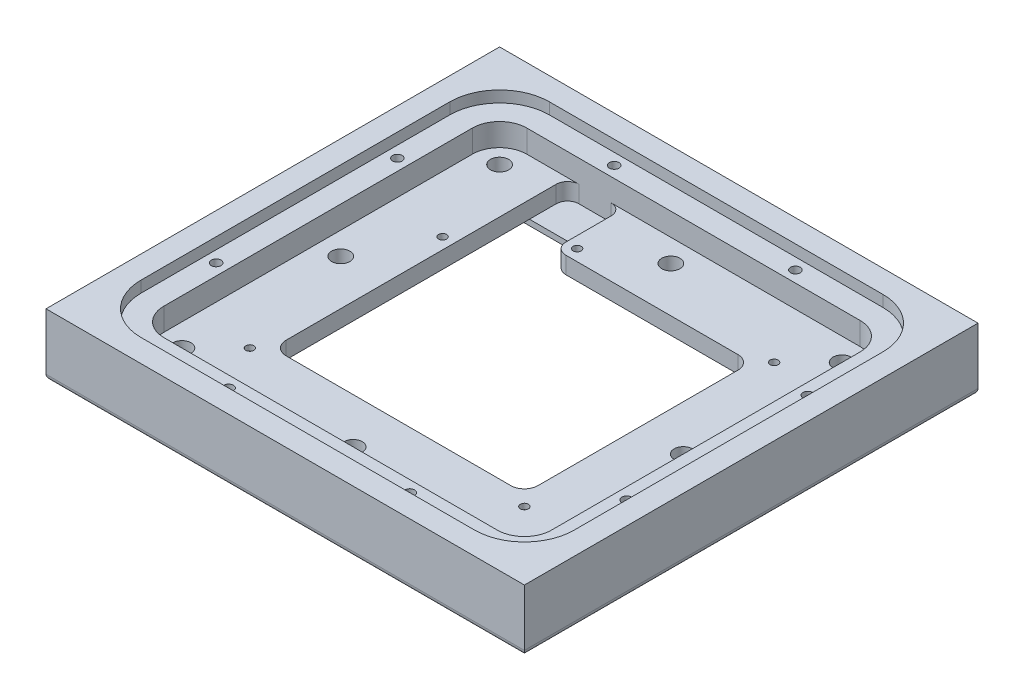
SolidWorks part; units mm, degrees
material "PE High Density"
ref_plane "Front Plane" through (0, 0, 0) normal (0, 0, 1) x (1, 0, 0)
ref_plane "Top Plane" through (0, 0, 0) normal (0, 1, 0) x (1, 0, 0)
ref_plane "Right Plane" through (0, 0, 0) normal (1, 0, 0) x (0, 0, -1)
sketch "Sketch2" plane through (0, 0, 0) normal (0, 1, 0) x (1, 0, 0)
  line L0 (-41.656, 22.1996) -> (-19.9136, 22.1996)
  line L1 (41.656, -38.1762) -> (-41.656, -38.1762)
  line L2 (41.656, -38.1762) -> (41.656, 38.1762)
  line L3 (41.656, 38.1762) -> (-41.656, 38.1762)
  line L4 (-41.656, -38.1762) -> (-41.656, 38.1762)
  line L5 (41.656, -38.1762) -> (-41.656, 38.1762) construction
  line L6 (41.656, 38.1762) -> (-41.656, -38.1762) construction
  line L7 (-19.9136, 22.1996) -> (-19.9136, 38.1762)
  line L8 (67.056, -63.5762) -> (-67.056, -63.5762)
  line L9 (-67.056, -63.5762) -> (-67.056, 63.5762)
  line L10 (67.056, 63.5762) -> (-67.056, 63.5762)
  line L11 (67.056, -63.5762) -> (67.056, 63.5762)
  point P0 (0, 0)
  point P13 (-38.481, -35.0012)
  point P14 (38.481, -35.0012)
  point P15 (38.481, 35.0012)
  point P16 (-16.7386, 35.0012)
  point P17 (-38.481, 19.0246)
  dimension "D1" = 83.312
  dimension "D2" = 76.3524
  dimension "D3" = 21.7424
  dimension "D4" = 15.9766
  dimension "D6" = 3.175
  dimension "D7" = 3.175
  dimension "D8" = 57.2008
  dimension "D9" = 80.137
  dimension "D10" = 24.9174
  dimension "D11" = 73.1774
  dimension "D5" = 25.4
extrude "Boss-Extrude1" add sketch "Sketch2" along normal blind 15.875 contours L8 L11 L10 L9 L1 L4 L3 L2 | L0 L7 L3 L4
sketch "Sketch4" plane through (0, 0, 0) normal (0, 1, 0) x (1, 0, 0)
  line L0 (41.656, -38.1762) -> (41.656, 38.1762) construction
  line L1 (41.656, 38.1762) -> (-19.9136, 38.1762) construction
  line L2 (41.656, -38.1762) -> (-41.656, -38.1762) construction
  line L3 (-41.656, -38.1762) -> (-41.656, 22.1996) construction
  line L4 (-41.656, 22.1996) -> (-19.9136, 22.1996) construction
  line L5 (41.656, -38.1762) -> (41.656, 38.1762)
  line L6 (41.656, 38.1762) -> (-19.9136, 38.1762)
  line L7 (41.656, -38.1762) -> (-41.656, -38.1762)
  line L8 (-41.656, -38.1762) -> (-41.656, 22.1996)
  line L9 (-41.656, 22.1996) -> (-19.9136, 22.1996)
  line L10 (-19.9136, 22.1996) -> (-19.9136, 38.1762) construction
  line L11 (-19.9136, 22.1996) -> (-19.9136, 38.1762)
  line L12 (35.306, 31.8262) -> (-13.5636, 31.8262)
  line L13 (-13.5636, 15.8496) -> (-13.5636, 31.8262)
  line L14 (-35.306, 15.8496) -> (-13.5636, 15.8496)
  line L15 (-35.306, -31.8262) -> (-35.306, 15.8496)
  line L16 (35.306, -31.8262) -> (-35.306, -31.8262)
  line L17 (35.306, -31.8262) -> (35.306, 31.8262)
  dimension "D1" = 6.35
extrude "Boss-Extrude2" add sketch "Sketch4" along normal blind 9.525
sketch "Sketch5" plane through (0, 0, 0) normal (0, -1, 0) x (1, 0, 0)
  line L5 (46.736, -50.8762) -> (-46.736, -50.8762)
  line L6 (54.356, -43.2562) -> (54.356, 43.2562)
  line L7 (46.736, 50.8762) -> (-46.736, 50.8762)
  line L8 (-54.356, -43.2562) -> (-54.356, 43.2562)
  line L9 (54.356, -50.8762) -> (-54.356, 50.8762) construction
  line L10 (54.356, 50.8762) -> (-54.356, -50.8762) construction
  arc A0 (46.736, -50.8762) -> (54.356, -43.2562) centre (46.736, -43.2562) ccw
  arc A1 (-46.736, -50.8762) -> (-54.356, -43.2562) centre (-46.736, -43.2562) cw
  arc A2 (54.356, 43.2562) -> (46.736, 50.8762) centre (46.736, 43.2562) ccw
  arc A3 (-46.736, 50.8762) -> (-54.356, 43.2562) centre (-46.736, 43.2562) ccw
  point P0 (0, 0)
  dimension "D3" = 7.62
  dimension "D1" = 108.712
  dimension "D2" = 101.7524
extrude "Cut-Extrude2" cut sketch "Sketch5" against normal blind 3.175
hole_wizard "M2.5x0.45 Tapped Hole1" positions "Sketch6" profile "Sketch7" tap size "M2.5x0.45" standard "ANSI Metric"
sketch "Sketch6" plane through (0, 3.175, 0) normal (0, -1, 0) x (-1, 0, 0)
  point P0 (38.481, -35.0012)
  point P3 (-38.481, -35.0012)
  point P6 (38.481, 19.0246)
  point P9 (16.7386, 35.0012)
  point P12 (-38.481, 35.0012)
sketch "Sketch7" plane through (-38.481, 3.175, 35.0012) normal (1, 0, 0) x (0, 0, -1)
  line L0 (0, 0) -> (0, 6.9659)
  line L1 (0, 6.9659) -> (1.025, 6.35)
  line L2 (1.025, 6.35) -> (1.025, 0)
  line L5 (1.025, 0) -> (0, 0)
  line L10 (0, 6.9659) -> (-1.025, 6.35) construction
  line L11 (0, -6.35) -> (0, 107.95) construction
  dimension "Tap Drill Dia." = 2.05
  dimension "Tap Drill Depth" = 6.35
  dimension "Drill Angle" = 118
cosmetic thread "Hole Thread1" parameters "D1"=5.08, "D2"=2.5
cosmetic thread "Hole Thread2" parameters "D1"=5.08, "D2"=2.5
cosmetic thread "Hole Thread3" parameters "D1"=5.08, "D2"=2.5
cosmetic thread "Hole Thread4" parameters "D1"=5.08, "D2"=2.5
cosmetic thread "Hole Thread5" parameters "D1"=5.08, "D2"=2.5
hole_wizard "#10 Clearance Hole1" positions "Sketch8" profile "Sketch9" hole size "#10" standard "ANSI Inch" end condition through all
sketch "Sketch8" plane through (0, 3.175, 0) normal (0, -1, 0) x (-1, 0, 0)
  line L0 (54.356, -43.2562) -> (54.356, 43.2562) construction
  line L1 (-46.736, -50.8762) -> (46.736, -50.8762) construction
  line L2 (46.736, 50.8762) -> (-46.736, 50.8762) construction
  line L3 (-54.356, 43.2562) -> (-54.356, -43.2562) construction
  point P0 (48.006, -44.5262)
  point P2 (0, -44.5262)
  point P4 (-48.006, -44.5262)
  point P6 (-48.006, 0)
  point P8 (-48.006, 44.5262)
  point P10 (0, 44.5262)
  point P12 (48.006, 44.5262)
  point P14 (48.006, 0)
  dimension "D1" = 6.35
  dimension "D2" = 6.35
  dimension "D3" = 6.35
  dimension "D4" = 6.35
sketch "Sketch9" plane through (-48.006, 3.175, 44.5262) normal (1, 0, 0) x (0, 0, -1)
  line L0 (0, 0) -> (0, 12.7)
  line L1 (0, 12.7) -> (2.5527, 12.7)
  line L2 (2.5527, 12.7) -> (2.5527, 0)
  line L5 (2.5527, 0) -> (0, 0)
  line L11 (0, -6.35) -> (0, 107.95) construction
  dimension "Thru Hole Dia." = 5.1054
  dimension "Thru Hole Depth" = 12.7
sketch "Sketch10" plane through (0, 15.875, 0) normal (0, 1, 0) x (1, 0, 0)
  line L4 (54.356, -43.2562) -> (54.356, 43.2562)
  line L5 (-46.736, -50.8762) -> (46.736, -50.8762)
  line L6 (-54.356, 43.2562) -> (-54.356, -43.2562)
  line L7 (46.736, 50.8762) -> (-46.736, 50.8762)
  line L8 (54.356, -43.2562) -> (54.356, 43.2562)
  line L9 (-46.736, -50.8762) -> (46.736, -50.8762)
  line L10 (-54.356, 43.2562) -> (-54.356, -43.2562)
  line L11 (46.736, 50.8762) -> (-46.736, 50.8762)
  arc A4 (54.356, 43.2562) -> (46.736, 50.8762) centre (46.736, 43.2562) ccw
  arc A5 (46.736, -50.8762) -> (54.356, -43.2562) centre (46.736, -43.2562) ccw
  arc A6 (-54.356, -43.2562) -> (-46.736, -50.8762) centre (-46.736, -43.2562) ccw
  arc A7 (-46.736, 50.8762) -> (-54.356, 43.2562) centre (-46.736, 43.2562) ccw
  arc A8 (54.356, 43.2562) -> (46.736, 50.8762) centre (46.736, 43.2562) ccw
  arc A9 (46.736, -50.8762) -> (54.356, -43.2562) centre (46.736, -43.2562) ccw
  arc A10 (-54.356, -43.2562) -> (-46.736, -50.8762) centre (-46.736, -43.2562) ccw
  arc A11 (-46.736, 50.8762) -> (-54.356, 43.2562) centre (-46.736, 43.2562) ccw
  dimension "D1" = 0
extrude "Cut-Extrude3" cut sketch "Sketch10" against normal up to surface (6.35 mm away) up to face at (-38.481, 9.525, 33.9762)
sketch "Sketch11" plane through (0, 3.175, 0) normal (0, -1, 0) x (1, 0, 0)
  line L8 (43.688, 40.2082) -> (-43.688, 40.2082)
  line L9 (-43.688, 40.2082) -> (-43.688, -40.2082)
  line L10 (-43.688, -40.2082) -> (43.688, -40.2082)
  line L11 (43.688, -40.2082) -> (43.688, 40.2082)
  line L12 (40.513, 40.2082) -> (-40.513, 40.2082)
  line L13 (-43.688, 37.0332) -> (-43.688, -37.0332)
  line L14 (-40.513, -40.2082) -> (40.513, -40.2082)
  line L15 (43.688, -37.0332) -> (43.688, 37.0332)
  arc A0 (40.513, -40.2082) -> (43.688, -37.0332) centre (40.513, -37.0332) ccw
  arc A1 (-43.688, -37.0332) -> (-40.513, -40.2082) centre (-40.513, -37.0332) ccw
  arc A2 (40.513, 40.2082) -> (43.688, 37.0332) centre (40.513, 37.0332) cw
  arc A3 (-40.513, 40.2082) -> (-43.688, 37.0332) centre (-40.513, 37.0332) ccw
  point P16 (-40.0685, 39.7637)
  point P17 (-40.0685, 39.7637)
  dimension "D2" = 3.175
  dimension "D1" = 2.032
extrude "Cut-Extrude4" cut sketch "Sketch11" against normal blind 1.6
sketch "Sketch12" plane through (0, 4.775, 0) normal (0, -1, 0) x (1, 0, 0)
  line L0 (-35.306, 31.8262) -> (-35.306, -15.8496) construction
  line L1 (35.306, 31.8262) -> (-35.306, 31.8262)
  line L2 (35.306, 31.8262) -> (35.306, -31.8262)
  line L3 (35.306, -31.8262) -> (-35.306, -31.8262)
  line L4 (-35.306, 31.8262) -> (-35.306, -31.8262)
  line L5 (-13.5636, -31.8262) -> (35.306, -31.8262) construction
extrude "Cut-Extrude5" cut sketch "Sketch12" against normal through all
fillet "Fillet1" radius 3.81 4 edges at (35.306, 7.15, -31.8262) (-35.306, 7.15, -31.8262) (35.306, 7.15, 31.8262) (-35.306, 7.15, 31.8262)
sketch "Sketch13" plane through (0, 0, 0) normal (0, -1, 0) x (1, 0, 0)
  line L4 (54.356, -43.2562) -> (54.356, 43.2562)
  line L5 (46.736, 50.8762) -> (-46.736, 50.8762)
  line L6 (-54.356, 43.2562) -> (-54.356, -43.2562)
  line L7 (-46.736, -50.8762) -> (46.736, -50.8762)
  line L8 (54.356, -43.2562) -> (54.356, 43.2562)
  line L9 (46.736, 50.8762) -> (-46.736, 50.8762)
  line L10 (-54.356, 43.2562) -> (-54.356, -43.2562)
  line L11 (-46.736, -50.8762) -> (46.736, -50.8762)
  line L12 (67.056, 63.5762) -> (-67.056, 63.5762)
  line L13 (-67.056, 63.5762) -> (-67.056, -63.5762)
  line L14 (-67.056, -63.5762) -> (67.056, -63.5762)
  line L15 (67.056, -63.5762) -> (67.056, 63.5762)
  line L16 (67.056, 63.5762) -> (-67.056, 63.5762)
  line L17 (-67.056, 63.5762) -> (-67.056, -63.5762)
  line L18 (-67.056, -63.5762) -> (67.056, -63.5762)
  line L19 (67.056, -63.5762) -> (67.056, 63.5762)
  arc A4 (46.736, -50.8762) -> (54.356, -43.2562) centre (46.736, -43.2562) ccw
  arc A5 (54.356, 43.2562) -> (46.736, 50.8762) centre (46.736, 43.2562) ccw
  arc A6 (-46.736, 50.8762) -> (-54.356, 43.2562) centre (-46.736, 43.2562) ccw
  arc A7 (-54.356, -43.2562) -> (-46.736, -50.8762) centre (-46.736, -43.2562) ccw
  arc A8 (46.736, -50.8762) -> (54.356, -43.2562) centre (46.736, -43.2562) ccw
  arc A9 (54.356, 43.2562) -> (46.736, 50.8762) centre (46.736, 43.2562) ccw
  arc A10 (-46.736, 50.8762) -> (-54.356, 43.2562) centre (-46.736, 43.2562) ccw
  arc A11 (-54.356, -43.2562) -> (-46.736, -50.8762) centre (-46.736, -43.2562) ccw
  dimension "D1" = 0
  dimension "D2" = 0
extrude "Cut-Extrude6" cut sketch "Sketch13" against normal blind 1.5875
fillet "Fillet2" radius 1.5875 4 edges at (67.056, 1.5875, 0) (0, 1.5875, 63.5762) (-67.056, 1.5875, 0) (0, 1.5875, -63.5762)
sketch "Sketch14" plane through (0, 9.525, 0) normal (0, 1, 0) x (1, 0, 0)
  line L1 (-35.306, 28.0162) -> (-19.9136, 28.0162)
  line L2 (-35.306, 28.0162) -> (-35.306, 50.8762)
  line L3 (-35.306, 50.8762) -> (-19.9136, 50.8762)
  line L4 (-19.9136, 28.0162) -> (-19.9136, 50.8762)
  line L6 (46.736, 50.8762) -> (-46.736, 50.8762) construction
  circle A0 centre (-16.7386, 35.0012) radius 1.025 construction
  dimension "D1" = 3.175
extrude "Cut-Extrude7" cut sketch "Sketch14" against normal up to surface (4.75 mm away) up to face at (0, 4.775, 0)
fillet "Fillet3" radius 3.175 3 edges at (-19.9136, 7.15, -50.8762) (-35.306, 7.15, -50.8762) (-19.9136, 7.15, -31.8262)
sketch "Sketch15" plane through (0, 15.875, 0) normal (0, 1, 0) x (1, 0, 0)
  line L0 (54.356, -43.2562) -> (54.356, 43.2562) construction
  line L1 (-46.736, -50.8762) -> (46.736, -50.8762) construction
  line L2 (-54.356, 43.2562) -> (-54.356, -43.2562) construction
  line L3 (46.736, 50.8762) -> (-46.736, 50.8762) construction
  line L4 (54.356, -43.2562) -> (54.356, 43.2562)
  line L5 (-46.736, -50.8762) -> (46.736, -50.8762)
  line L6 (-54.356, 43.2562) -> (-54.356, -43.2562)
  line L7 (46.736, 50.8762) -> (-46.736, 50.8762)
  line L8 (60.706, -43.2562) -> (60.706, 43.2562)
  line L9 (46.736, 57.2262) -> (-46.736, 57.2262)
  line L10 (-60.706, 43.2562) -> (-60.706, -43.2562)
  line L11 (-46.736, -57.2262) -> (46.736, -57.2262)
  line L16 (-67.056, -63.5762) -> (67.056, -63.5762)
  line L17 (67.056, -63.5762) -> (67.056, 63.5762)
  line L18 (67.056, 63.5762) -> (-67.056, 63.5762)
  line L19 (-67.056, 63.5762) -> (-67.056, -63.5762)
  line L20 (-67.056, -63.5762) -> (67.056, -63.5762)
  line L21 (67.056, -63.5762) -> (67.056, 63.5762)
  line L22 (67.056, 63.5762) -> (-67.056, 63.5762)
  line L23 (-67.056, 63.5762) -> (-67.056, -63.5762)
  arc A0 (46.736, -50.8762) -> (54.356, -43.2562) centre (46.736, -43.2562) ccw construction
  arc A1 (-54.356, -43.2562) -> (-46.736, -50.8762) centre (-46.736, -43.2562) ccw construction
  arc A2 (54.356, 43.2562) -> (46.736, 50.8762) centre (46.736, 43.2562) ccw construction
  arc A3 (-46.736, 50.8762) -> (-54.356, 43.2562) centre (-46.736, 43.2562) ccw construction
  arc A4 (46.736, -50.8762) -> (54.356, -43.2562) centre (46.736, -43.2562) ccw
  arc A5 (-54.356, -43.2562) -> (-46.736, -50.8762) centre (-46.736, -43.2562) ccw
  arc A6 (54.356, 43.2562) -> (46.736, 50.8762) centre (46.736, 43.2562) ccw
  arc A7 (-46.736, 50.8762) -> (-54.356, 43.2562) centre (-46.736, 43.2562) ccw
  arc A8 (60.706, 43.2562) -> (46.736, 57.2262) centre (46.736, 43.2562) ccw
  arc A9 (-46.736, 57.2262) -> (-60.706, 43.2562) centre (-46.736, 43.2562) ccw
  arc A10 (-60.706, -43.2562) -> (-46.736, -57.2262) centre (-46.736, -43.2562) ccw
  arc A11 (46.736, -57.2262) -> (60.706, -43.2562) centre (46.736, -43.2562) ccw
  line M29 (-67.056, -63.5762) -> (67.056, -63.5762)
  line M30 (67.056, -63.5762) -> (67.056, 63.5762)
  line M31 (67.056, 63.5762) -> (-67.056, 63.5762)
  line M32 (-67.056, 63.5762) -> (-67.056, -63.5762)
  dimension "D1" = 6.35
  dimension "D2" = 0
extrude "Boss-Extrude3" add sketch "Sketch15" along normal blind 3.175 contours A11 L11 A10 L10 A9 L9 A8 L8 M32 M29 M30 M31
hole_wizard "#6-32 Tapped Hole1" positions "Sketch16" profile "Sketch18" tap size "#6-32" standard "ANSI Inch"
sketch "Sketch16" plane through (0, 15.875, 0) normal (0, 1, 0) x (1, 0, 0)
  line L28 (57.531, -43.2562) -> (57.531, 43.2562)
  line L29 (-46.736, -54.0512) -> (46.736, -54.0512)
  line L30 (-57.531, 43.2562) -> (-57.531, -43.2562)
  line L31 (46.736, 54.0512) -> (-46.736, 54.0512)
  line L32 (57.531, -43.2562) -> (57.531, 43.2562) construction
  line L33 (-46.736, -54.0512) -> (46.736, -54.0512) construction
  line L34 (-57.531, 43.2562) -> (-57.531, -43.2562) construction
  line L35 (46.736, 54.0512) -> (-46.736, 54.0512) construction
  arc A24 (57.531, 43.2562) -> (46.736, 54.0512) centre (46.736, 43.2562) ccw
  arc A25 (46.736, -54.0512) -> (57.531, -43.2562) centre (46.736, -43.2562) ccw
  arc A26 (-57.531, -43.2562) -> (-46.736, -54.0512) centre (-46.736, -43.2562) ccw
  arc A27 (-46.736, 54.0512) -> (-57.531, 43.2562) centre (-46.736, 43.2562) ccw
  arc A28 (57.531, 43.2562) -> (46.736, 54.0512) centre (46.736, 43.2562) ccw construction
  arc A29 (46.736, -54.0512) -> (57.531, -43.2562) centre (46.736, -43.2562) ccw construction
  arc A30 (-57.531, -43.2562) -> (-46.736, -54.0512) centre (-46.736, -43.2562) ccw construction
  arc A31 (-46.736, 54.0512) -> (-57.531, 43.2562) centre (-46.736, 43.2562) ccw construction
  point P141 (-25.4, 54.0512)
  point P143 (-57.531, 25.4)
  point P145 (-57.531, -25.4)
  point P147 (-25.4, -54.0512)
  dimension "D2" = 25.4
  dimension "D3" = 25.4
  dimension "D4" = 25.4
  dimension "D1" = 3.175
cosmetic thread "Hole Thread6" parameters "D1"=14.224, "D2"=3.5052
cosmetic thread "Hole Thread7" parameters "D1"=14.224, "D2"=3.5052
cosmetic thread "Hole Thread8" parameters "D1"=14.224, "D2"=3.5052
cosmetic thread "Hole Thread9" parameters "D1"=14.224, "D2"=3.5052
sketch "Sketch18" plane through (-25.4, 15.875, 54.0512) normal (1, 0, 0) x (0, 0, 1)
  line L0 (0, 0) -> (0, 10.3377)
  line L1 (0, 10.3377) -> (1.3525, 9.525)
  line L2 (1.3525, 9.525) -> (1.3525, 0)
  line L5 (1.3525, 0) -> (0, 0)
  line L10 (0, 10.3377) -> (-1.3526, 9.525) construction
  line L11 (0, -6.35) -> (0, 107.95) construction
  dimension "Tap Drill Dia." = 2.7051
  dimension "Tap Drill Depth" = 9.525
  dimension "Drill Angle" = 118
mirror "Mirror1" about plane through (0, 0, 0) normal (1, 0, 0) of "#6-32 Tapped Hole1"
cosmetic thread "Hole Thread10" parameters "D1"=14.224, "D2"=3.5052
cosmetic thread "Hole Thread11" parameters "D1"=14.224, "D2"=3.5052
cosmetic thread "Hole Thread12" parameters "D1"=14.224, "D2"=3.5052
cosmetic thread "Hole Thread13" parameters "D1"=14.224, "D2"=3.5052
sketch "Sketch19" plane through (0, 4.775, 0) normal (0, -1, 0) x (1, 0, 0)
  circle A0 centre (38.481, 35.0012) radius 2.7813
  circle A1 centre (38.481, -35.0012) radius 2.7813
  circle A2 centre (-38.481, 35.0012) radius 2.7813
  circle A3 centre (-38.481, -19.0246) radius 2.7813
  circle A4 centre (-16.7386, -35.0012) radius 2.7813
  point P0 (38.481, 35.0012)
  dimension "D1" = 5.5626
  dimension "D2" = 5.5626
  dimension "D3" = 5.5626
  dimension "D4" = 5.5626
  dimension "D5" = 5.5626
extrude "Cut-Extrude8" cut sketch "Sketch19" against normal blind 3.175
hole_wizard "#4-40 Tapped Hole1" positions "Sketch20" profile "Sketch21" tap size "#4-40" standard "ANSI Inch"
sketch "Sketch20" plane through (0, 9.525, 0) normal (0, 1, 0) x (1, 0, 0)
  point P0 (-38.481, 19.0246)
  point P3 (-16.7386, 35.0012)
  point P6 (38.481, 35.0012)
  point P9 (38.481, -35.0012)
  point P12 (-38.481, -35.0012)
sketch "Sketch21" plane through (-38.481, 9.525, -19.0246) normal (1, 0, 0) x (0, 0, 1)
  line L0 (0, 0) -> (0, 8.2992)
  line L1 (0, 8.2992) -> (1.1303, 7.62)
  line L2 (1.1303, 7.62) -> (1.1303, 0)
  line L5 (1.1303, 0) -> (0, 0)
  line L10 (0, 8.2992) -> (-1.1303, 7.62) construction
  line L11 (0, -6.35) -> (0, 107.95) construction
  dimension "Tap Drill Dia." = 2.2606
  dimension "Tap Drill Depth" = 7.62
  dimension "Drill Angle" = 118
cosmetic thread "Hole Thread14" parameters "D1"=5.588, "D2"=2.8448
cosmetic thread "Hole Thread15" parameters "D1"=5.588, "D2"=2.8448
cosmetic thread "Hole Thread16" parameters "D1"=5.588, "D2"=2.8448
cosmetic thread "Hole Thread17" parameters "D1"=5.588, "D2"=2.8448
cosmetic thread "Hole Thread18" parameters "D1"=5.588, "D2"=2.8448
equation "\"D3@Sketch16\"=\"D2@Sketch16\""
equation "\"D4@Sketch16\"=\"D2@Sketch16\""
